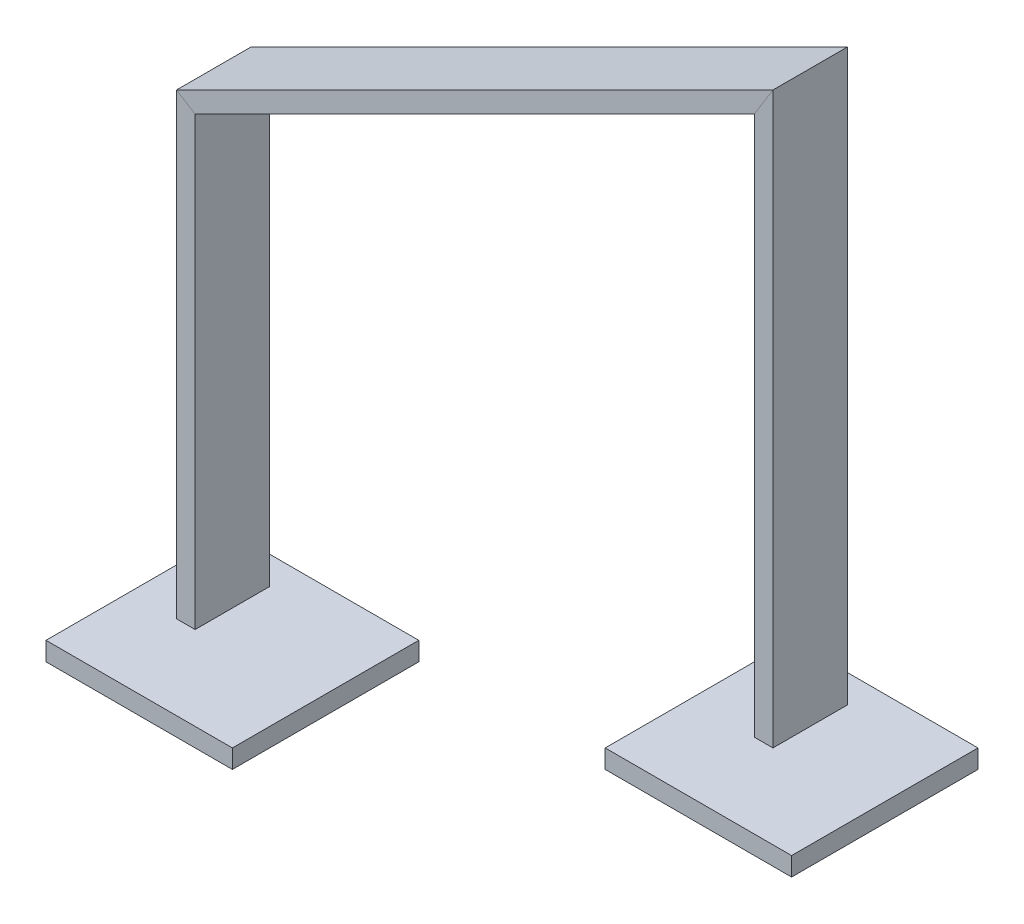
SolidWorks part; units mm, degrees
ref_plane "Front" through (0, 0, 0) normal (0, 0, 1) x (1, 0, 0)
ref_plane "Top" through (0, 0, 0) normal (0, 1, 0) x (1, 0, 0)
ref_plane "Right" through (0, 0, 0) normal (1, 0, 0) x (0, 0, -1)
sketch "Skizze1" plane through (0, 0, 0) normal (0, 1, 0) x (1, 0, 0)
  line L1 (0, -50) -> (100, -50)
  line L2 (0, -50) -> (0, 50)
  line L3 (0, 50) -> (100, 50)
  line L4 (100, -50) -> (100, 50)
  dimension "D1" = 100
  dimension "D2" = 50
  dimension "D3" = 0
extrude "Aufsatz-Linear austragen1" add sketch "Skizze1" along normal blind 10
sketch "Skizze2" plane through (0, 0, 0) normal (0, 0, 1) x (1, 0, 0)
  line L0 (0, 10) -> (100, 10) construction
  line L1 (300, 100) -> (400, 100)
  line L2 (300, 100) -> (300, 110)
  line L3 (300, 110) -> (400, 110)
  line L4 (400, 100) -> (400, 110)
  line L5 (100, 10) -> (100, 0) construction
  dimension "D1" = 10
  dimension "D2" = 100
  dimension "D3" = 100
  dimension "D4" = 300
extrude "Aufsatz-Linear austragen2" add sketch "Skizze2" along normal mid plane 100 separate body
sketch "Skizze3" plane through (0, 0, 0) normal (0, 0, 1) x (1, 0, 0)
  line L0 (50, 25) -> (50, 264.5085)
  line L1 (50, 264.5085) -> (350, 414.5085)
  line L2 (350, 414.5085) -> (350, 125)
  line L3 (0, 10) -> (0, 0) construction
  line L4 (300, 110) -> (300, 100) construction
  line L5 (0, 10) -> (100, 10) construction
  line L6 (400, 110) -> (300, 110) construction
  line L7 (100, 10) -> (300, 110) construction
  point P14 (0, 0)
  point P15 (50, 25)
  dimension "D1" = 50
  dimension "D2" = 50
  dimension "D3" = 15
  dimension "D4" = 15
  dimension "D5" = 250
sketch "Skizze4" plane through (0, 10, 0) normal (0, 1, 0) x (1, 0, 0)
  line L1 (50, -20) -> (40, -20)
  line L2 (50, -20) -> (50, 20)
  line L3 (50, 20) -> (40, 20)
  line L4 (40, -20) -> (40, 20)
  point P0 (50, 0)
  point P6 (50, 0)
  dimension "D1" = 40
  dimension "D2" = 10
ref_plane "Ebene1" through (50, 25, 0) normal (0, 1, 0) x (1, 0, 0)
sketch "Skizze5" plane through (0, 25, 0) normal (0, 1, 0) x (1, 0, 0)
  line L0 (50, -20) -> (50, 20) construction
  line L1 (50, -20) -> (40, -20)
  line L2 (50, -20) -> (50, 20)
  line L3 (50, 20) -> (40, 20)
  line L4 (40, -20) -> (40, 20)
  point P0 (50, 0)
sweep "Austragung2" add profiles "Skizze5" path "Skizze3"
